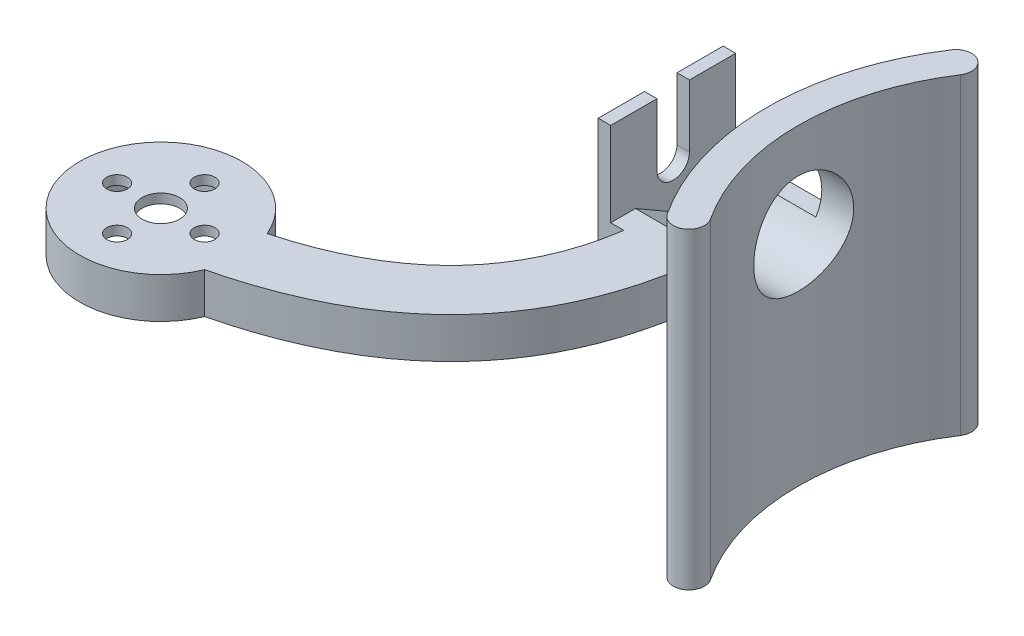
SolidWorks part; units mm, degrees
ref_plane "Plan de face" through (0, 0, 0) normal (0, 0, 1) x (1, 0, 0)
ref_plane "Plan de dessus" through (0, 0, 0) normal (0, 1, 0) x (1, 0, 0)
ref_plane "Plan de droite" through (0, 0, 0) normal (1, 0, 0) x (0, 0, -1)
sketch "Esquisse1" plane through (0, 0, 0) normal (0, 1, 0) x (1, 0, 0)
  line L0 (-30.5328, 20) -> (-30.5328, -20) construction
  line L1 (-30.5328, 0) -> (0, 0) construction
  circle A0 centre (0, 0) radius 36.5 construction
  arc A2 (-32.6241, -21.3699) -> (-32.6241, 21.3699) centre (0, 0) cw construction
  arc A3 (-34.7153, 22.7397) -> (-34.7153, -22.7397) centre (0, 0) ccw
  arc A4 (-30.5328, 20) -> (-30.5328, -20) centre (0, 0) ccw
  arc A5 (-30.5328, 20) -> (-34.7153, 22.7397) centre (-32.6241, 21.3699) ccw
  arc A6 (-34.7153, -22.7397) -> (-30.5328, -20) centre (-32.6241, -21.3699) ccw
  point P9 (-39, 0)
  dimension "D1" = 73
  dimension "D3" = 2.5
  dimension "D2" = 40
extrude "Boss.-Extru.1" add sketch "Esquisse1" along normal blind 50
sketch "Esquisse2" plane through (0, 0, 0) normal (1, 0, 0) x (0, 0, -1)
  line L0 (0, 35) -> (0, 0) construction
  circle A0 centre (0, 35) radius 8
  dimension "D1" = 16
  dimension "D2" = 35
extrude "Enlèv. mat.-Extru.1" cut sketch "Esquisse2" against normal through all
ref_plane "Plan1" through (-41.5, 0, 0) normal (-1, 0, 0) x (0, 0, 1)
ref_plane "Plan2" through (-56.5, 0, 0) normal (-1, 0, 0) x (0, 0, 1)
sketch "Esquisse4" plane through (-56.5, 0, 0) normal (-1, 0, 0) x (0, 0, 1)
  line L0 (-2.6, 35) -> (-2.6, 45)
  line L1 (-10, 25) -> (10, 25)
  line L2 (-10, 25) -> (-10, 45)
  line L3 (-10, 45) -> (10, 45) construction
  line L4 (10, 25) -> (10, 45)
  line L5 (-10, 25) -> (10, 45) construction
  line L6 (-10, 45) -> (10, 25) construction
  line L7 (2.6, 35) -> (2.6, 45)
  line L8 (-10, 45) -> (-2.6, 45)
  line L9 (2.6, 45) -> (10, 45)
  circle A0 centre (0, 35) radius 2.6 construction
  arc A1 (-2.6, 35) -> (2.6, 35) centre (0, 35) ccw
  dimension "D1" = 5.2
  dimension "D2" = 20
extrude "Boss.-Extru.3" add sketch "Esquisse4" along normal blind 2 separate body
sketch "Esquisse6" plane through (-56.5, 0, 0) normal (-1, 0, 0) x (0, 0, 1)
  line L0 (-6.05, 31.507) -> (-6.05, 38.493) construction
  line L1 (-6.05, 38.493) -> (0, 41.9859) construction
  line L2 (0, 41.9859) -> (6.05, 38.493) construction
  line L3 (6.05, 38.493) -> (6.05, 31.507) construction
  line L4 (6.05, 31.507) -> (0, 28.0141)
  line L5 (0, 28.0141) -> (-6.05, 31.507)
  line L6 (-6.05, 38.493) -> (6.05, 38.493) construction
  line L7 (-6.05, 38.493) -> (6.05, 31.507) construction
  line L8 (-6.05, 31.507) -> (-10, 31.507)
  line L9 (-10, 45) -> (-10, 25) construction
  line L10 (-10, 31.507) -> (-10, 25)
  line L11 (-10, 25) -> (10, 25)
  line L12 (10, 25) -> (10, 31.507)
  line L13 (10, 25) -> (10, 45) construction
  line L14 (10, 31.507) -> (6.05, 31.507)
  line L15 (-10, 25) -> (10, 25) construction
  point P4 (0, 35)
  point P7 (0, 35)
  dimension "D1" = 12.1
  dimension "D2" = 120
extrude "Boss.-Extru.4" add sketch "Esquisse6" against normal blind 8
sketch "Esquisse7" plane through (-48.5, 0, 0) normal (1, 0, 0) x (0, 0, -1)
  line L0 (-7.1972, 31.507) -> (7.1972, 31.507) construction
  line L2 (6.05, 31.507) -> (10, 31.507) construction
  line L3 (7.1972, 31.507) -> (10, 31.507)
  line L4 (10, 31.507) -> (10, 25)
  line L5 (10, 25) -> (-10, 25)
  line L6 (-10, 25) -> (-10, 31.507)
  line L7 (-10, 31.507) -> (-7.1972, 31.507)
  line L9 (10, 25) -> (-10, 25) construction
  circle A0 centre (0, 35) radius 8 construction
  arc A1 (-7.1972, 31.507) -> (7.1972, 31.507) centre (0, 35) ccw
  dimension "D1" = 16
  dimension "D2" = 20
extrude "Boss.-Extru.5" add sketch "Esquisse7" along normal up to surface (7.6289 mm away)
sketch "Esquisse8" plane through (0, 25, 0) normal (0, -1, 0) x (1, 0, 0)
  line L0 (-58.5, 0) -> (-94.5001, 0) construction
  line L2 (-94.5001, 0) -> (-94.5001, 44) construction
  line L4 (-58.0357, 21.4645) -> (-50.9646, 28.5355) construction
  line L6 (-54.5001, 25) -> (-54.5001, 0) construction
  line L7 (-54.5001, 25) -> (-94.5001, 25) construction
  line L8 (-82.5001, 39) -> (-82.5001, 49) construction
  line L9 (-94.5001, 44) -> (-87.5001, 44) construction
  line L10 (-58.5, -10) -> (-58.5, 10) construction
  line L11 (-40.2772, 10) -> (-58.5, 10) construction
  line L12 (-54.3886, 10) -> (-44.3886, 10)
  line L13 (-87.5001, 44) -> (-82.5001, 44) construction
  circle A0 centre (-94.5001, 44) radius 13 construction
  arc A1 (-82.5001, 49) -> (-82.5001, 39) centre (-94.5001, 44) ccw
  circle A2 centre (-87.5001, 44) radius 1.65
  circle A3 centre (-94.5001, 37) radius 1.65
  circle A4 centre (-101.5001, 44) radius 1.65
  circle A5 centre (-94.5001, 51) radius 1.65
  circle A6 centre (-94.5001, 44) radius 3
  spline S0 degree 2 poles (-82.5001, 39) (-57.709, 32.3018) (-54.3886, 10) knots 0 0 0 1 1 1
  spline S3 degree 2 poles (-82.5001, 49) (-49.0005, 40.8974) (-44.3886, 10) knots 0 0 0 1 1 1
  point P10 (-49.3886, 10)
  point P11 (-94.5001, 44)
  point P30 (-94.5001, 44)
  point P43 (-49.3886, 10)
  dimension "D4" = 26
  dimension "D8" = 3.3
  dimension "D11" = 6
  dimension "D1" = 36.0001
  dimension "D2" = 44
  dimension "D3" = 10
  dimension "D5" = 40
  dimension "D6" = 25
  dimension "D7" = 45
  dimension "D9" = 7
  dimension "D10" = 4
extrude "Boss.-Extru.6" add sketch "Esquisse8" against normal up to surface (6.507 mm away) up to face at (-48.5288, 31.507, 7.7499)
sketch "Esquisse9" plane through (0, 25, 0) normal (0, -1, 0) x (1, 0, 0)
  circle A0 centre (-94.5001, 44) radius 10.5
  dimension "D1" = 21
extrude "Enlèv. mat.-Extru.2" cut sketch "Esquisse9" against normal offset from surface (5.007 mm away) 1.5 up to face at (-58.495, 31.507, 15.9499)
